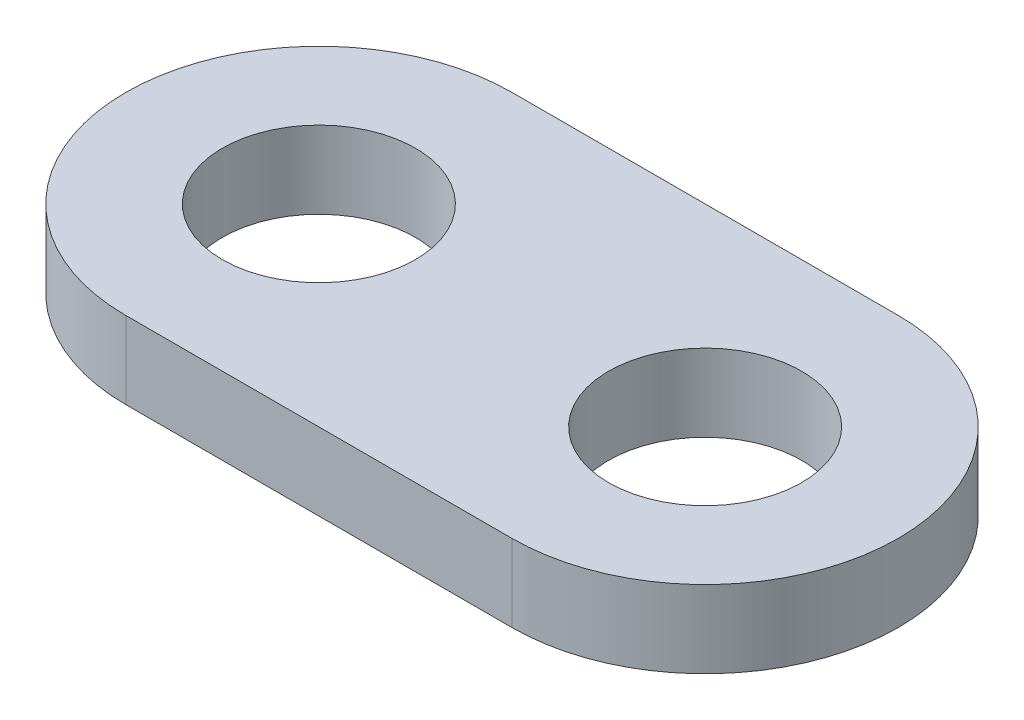
SolidWorks part; units mm, degrees
ref_plane "Front Plane" through (0, 0, 0) normal (0, 0, 1) x (1, 0, 0)
ref_plane "Top Plane" through (0, 0, 0) normal (0, 1, 0) x (1, 0, 0)
ref_plane "Right Plane" through (0, 0, 0) normal (1, 0, 0) x (0, 0, -1)
sketch "Sketch1" plane through (0, 0, 0) normal (0, 1, 0) x (1, 0, 0)
  line L0 (-6.35, 0) -> (6.35, 0) construction
  line L1 (-6.35, 6.35) -> (6.35, 6.35)
  line L2 (-6.35, -6.35) -> (6.35, -6.35)
  arc A0 (-6.35, 6.35) -> (-6.35, -6.35) centre (-6.35, 0) ccw
  arc A1 (6.35, -6.35) -> (6.35, 6.35) centre (6.35, 0) ccw
  circle A2 centre (-6.35, 0) radius 3.175
  circle A3 centre (6.35, 0) radius 3.175
  point P3 (0, 0)
  dimension "D1" = 6.35
  dimension "D2" = 3.175
  dimension "D3" = 12.7
extrude "Boss-Extrude1" add sketch "Sketch1" along normal blind 2.54
